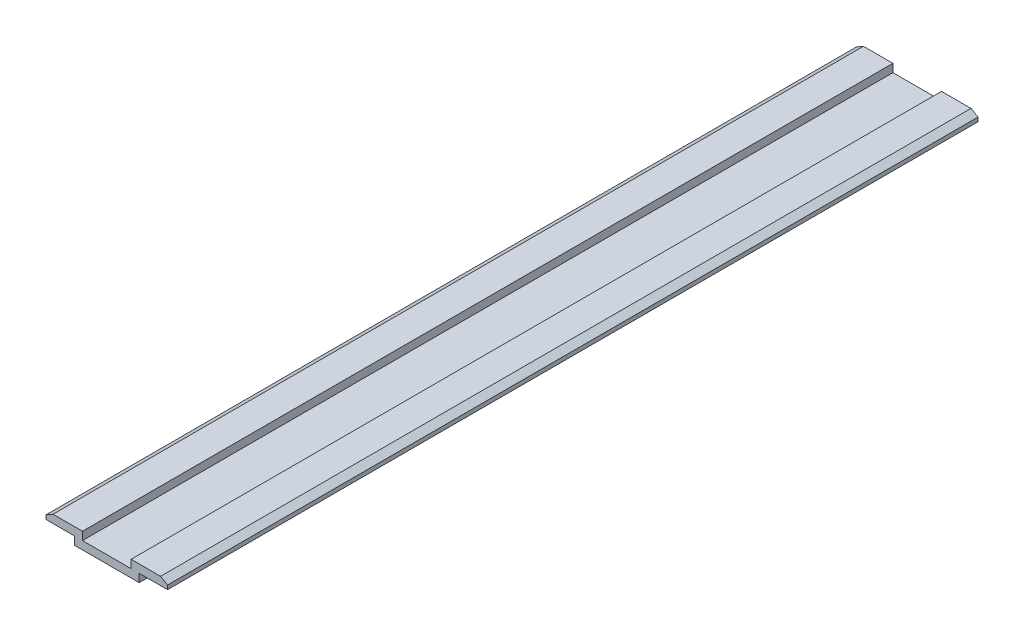
SolidWorks part; units mm, degrees
ref_plane "Plano frontal" through (0, 0, 0) normal (0, 0, 1) x (1, 0, 0)
ref_plane "Plano superior" through (0, 0, 0) normal (0, 1, 0) x (1, 0, 0)
ref_plane "Plano direito" through (0, 0, 0) normal (1, 0, 0) x (0, 0, -1)
sketch "Esboço1" plane through (0, 0, 0) normal (0, 0, 1) x (1, 0, 0)
  line L0 (0, 0) -> (0, 9.5399) construction
  line L1 (4, 0) -> (-4, 0)
  line L2 (-4, 0) -> (-4, 1)
  line L3 (-4, 1) -> (-7.5, 1)
  line L4 (-7.5, 1) -> (-7.5, 1.5)
  line L5 (7.5, 1) -> (7.5, 1.5)
  line L6 (4, 1) -> (7.5, 1)
  line L7 (4, 0) -> (4, 1)
  line L8 (6.634, 2) -> (6.634, 2)
  line L9 (3, 2) -> (6.634, 2)
  line L10 (3, 1) -> (3, 2)
  line L11 (3, 1) -> (-3, 1)
  line L12 (-3, 1) -> (-3, 2)
  line L13 (-3, 2) -> (-6.634, 2)
  line L14 (-6.634, 2) -> (-6.634, 2)
  line L15 (7.5, 1.5) -> (6.634, 2)
  line L16 (-7.5, 1.5) -> (-6.634, 2)
  dimension "D1" = 8
  dimension "D2" = 1
  dimension "D3" = 15
  dimension "D4" = 1.5
  dimension "D5" = 0
  dimension "D6" = 1
extrude "Ressalto-extrusão1" add sketch "Esboço1" along normal blind 100
